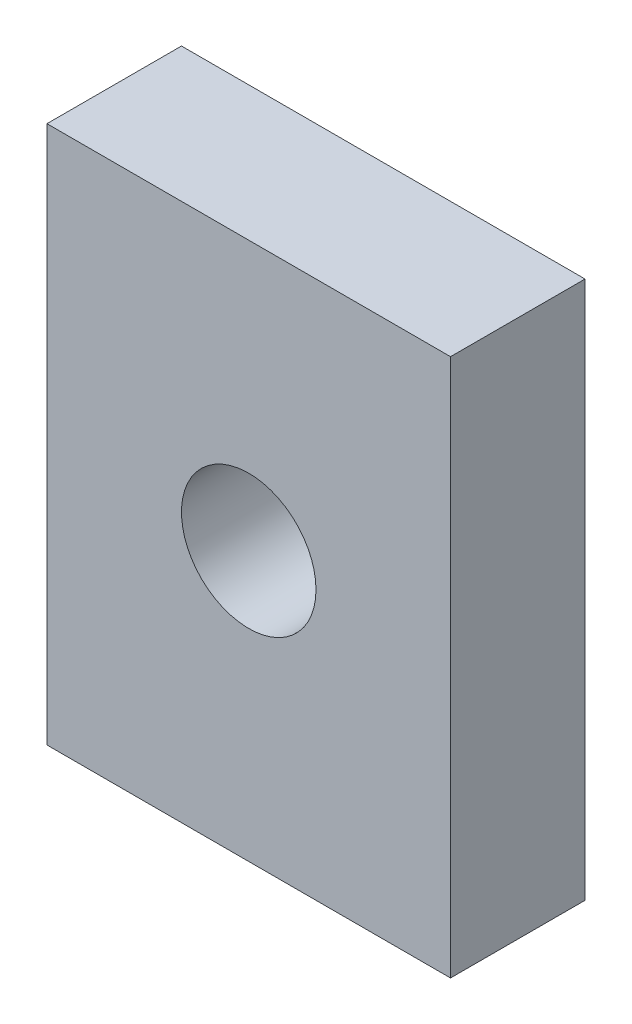
SolidWorks part; units mm, degrees
ref_plane "Plano frontal" through (0, 0, 0) normal (0, 0, 1) x (1, 0, 0)
ref_plane "Plano superior" through (0, 0, 0) normal (0, 1, 0) x (1, 0, 0)
ref_plane "Plano direito" through (0, 0, 0) normal (1, 0, 0) x (0, 0, -1)
sketch "Esboço1" plane through (0, 0, 0) normal (0, 0, 1) x (1, 0, 0)
  line L1 (7.5, -10) -> (-7.5, -10)
  line L2 (7.5, -10) -> (7.5, 10)
  line L3 (7.5, 10) -> (-7.5, 10)
  line L4 (-7.5, -10) -> (-7.5, 10)
  line L5 (7.5, -10) -> (-7.5, 10) construction
  line L6 (7.5, 10) -> (-7.5, -10) construction
  circle A0 centre (0, 0) radius 2.5
  point P0 (0, 0)
  dimension "D3" = 5
  dimension "D1" = 15
  dimension "D2" = 20
extrude "Ressalto-extrusão1" add sketch "Esboço1" along normal blind 5
